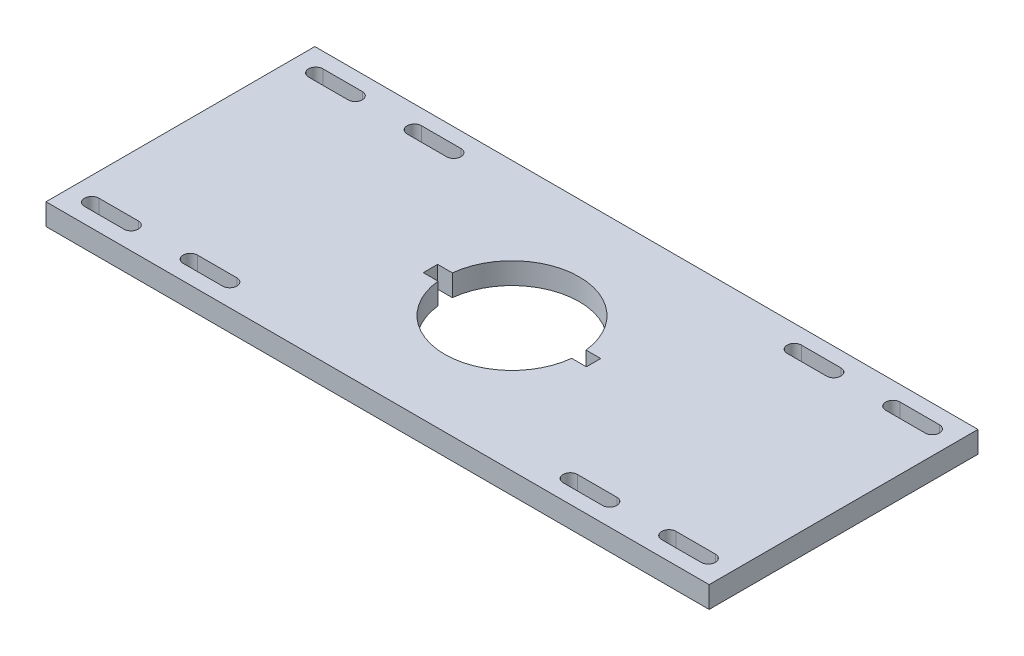
SolidWorks part; units mm, degrees
material "PA Type 6"
ref_plane "Front Plane" through (0, 0, 0) normal (0, 0, 1) x (1, 0, 0)
ref_plane "Top Plane" through (0, 0, 0) normal (0, 1, 0) x (1, 0, 0)
ref_plane "Right Plane" through (0, 0, 0) normal (1, 0, 0) x (0, 0, -1)
sketch "Sketch1" plane through (0, 0, 0) normal (0, 1, 0) x (1, 0, 0)
  line L1 (-185, 75) -> (185, 75)
  line L2 (-185, 75) -> (-185, -75)
  line L3 (-185, -75) -> (185, -75)
  line L4 (185, 75) -> (185, -75)
  line L5 (-185, 75) -> (185, -75) construction
  line L6 (-185, -75) -> (185, 75) construction
  point P0 (0, 0)
  dimension "D1" = 150
  dimension "D2" = 370
extrude "Boss-Extrude1" add sketch "Sketch1" along normal blind 12
sketch "Sketch3" plane through (0, 12, 0) normal (0, 1, 0) x (1, 0, 0)
  circle A0 centre (0, 0) radius 37.5
  dimension "D1" = 75
extrude "Cut-Extrude2" cut sketch "Sketch3" against normal through all
sketch "Sketch4" plane through (0, 0, 0) normal (0, -1, 0) x (-1, 0, 0)
  circle A0 centre (0, 0) radius 60
  circle A1 centre (0, 0) radius 37.5 construction
  circle A2 centre (0, 0) radius 37.5
  dimension "D1" = 120
extrude "Boss-Extrude2" [suppressed] add sketch "Sketch4" along normal blind 0.01
sketch "Sketch5" plane through (0, 12, 0) normal (0, 1, 0) x (1, 0, 0)
  line L0 (185, -75) -> (185, 75) construction
  line L1 (185, -65) -> (106.9302, -65)
  line L2 (185, -65) -> (185, 75)
  line L3 (185, 75) -> (106.9302, 75)
  line L4 (106.9302, -65) -> (106.9302, 75)
  line L5 (185, 75) -> (-185, 75) construction
  line L6 (5, 0) -> (5, -106.4308) construction
  line L7 (-96.9302, -65) -> (-96.9302, 75)
  line L8 (-175, 75) -> (-96.9302, 75)
  line L9 (-175, -65) -> (-175, 75)
  line L10 (-175, -65) -> (-96.9302, -65)
extrude "Boss-Extrude3" [suppressed] add sketch "Sketch5" along normal blind 0.01
sketch "Sketch6" plane through (0, 12, 0) normal (0, 1, 0) x (1, 0, 0)
  line L1 (45.5, -4) -> (-45.5, -4)
  line L2 (45.5, -4) -> (45.5, 4)
  line L3 (45.5, 4) -> (-45.5, 4)
  line L4 (-45.5, -4) -> (-45.5, 4)
  line L5 (45.5, -4) -> (-45.5, 4) construction
  line L6 (45.5, 4) -> (-45.5, -4) construction
  circle A0 centre (0, 0) radius 37.5 construction
  point P0 (0, 0)
  point P8 (-37.5, 0)
  dimension "D2" = 8
  dimension "D1" = 8
extrude "Cut-Extrude3" cut sketch "Sketch6" against normal through all
sketch "Sketch7" plane through (0, 12, 0) normal (0, 1, 0) x (1, 0, 0)
  line L0 (-95, -62.5) -> (-117, -62.5) construction
  line L1 (-95, -66.5) -> (-117, -66.5)
  line L2 (-95, -58.5) -> (-117, -58.5)
  line L3 (-150, -62.5) -> (-172, -62.5) construction
  line L4 (-150, -66.5) -> (-172, -66.5)
  line L5 (-150, -58.5) -> (-172, -58.5)
  line L6 (0, 0) -> (-217.0589, 0) construction
  line L7 (-150, 62.5) -> (-172, 62.5) construction
  line L8 (-150, 66.5) -> (-172, 66.5)
  line L9 (-150, 58.5) -> (-172, 58.5)
  line L10 (-95, 62.5) -> (-117, 62.5) construction
  line L11 (-95, 66.5) -> (-117, 66.5)
  line L12 (-95, 58.5) -> (-117, 58.5)
  circle A0 centre (-95, -62.5) radius 4
  arc A1 (-95, -66.5) -> (-95, -58.5) centre (-95, -62.5) ccw
  arc A2 (-117, -58.5) -> (-117, -66.5) centre (-117, -62.5) ccw
  arc A3 (-150, -66.5) -> (-150, -58.5) centre (-150, -62.5) ccw
  arc A4 (-172, -58.5) -> (-172, -66.5) centre (-172, -62.5) ccw
  arc A5 (-150, 66.5) -> (-150, 58.5) centre (-150, 62.5) cw
  arc A6 (-172, 58.5) -> (-172, 66.5) centre (-172, 62.5) cw
  arc A7 (-95, 66.5) -> (-95, 58.5) centre (-95, 62.5) cw
  arc A8 (-117, 58.5) -> (-117, 66.5) centre (-117, 62.5) cw
  point P4 (-106, -62.5)
  point P13 (-161, -62.5)
  point P20 (-161, 62.5)
  point P27 (-106, 62.5)
  dimension "D1" = 8
  dimension "D2" = 62.5
  dimension "D3" = 95
  dimension "D4" = 22
  dimension "D5" = 2
extrude "Cut-Extrude4" cut sketch "Sketch7" against normal through all contours L5 A4 L4 A3 | A6 L9 A5 L8 | A8 L12 A7 L11 | L2 A2 L1 A1
mirror "Mirror1" about plane through (0, 0, 0) normal (1, 0, 0) of "Cut-Extrude4"
